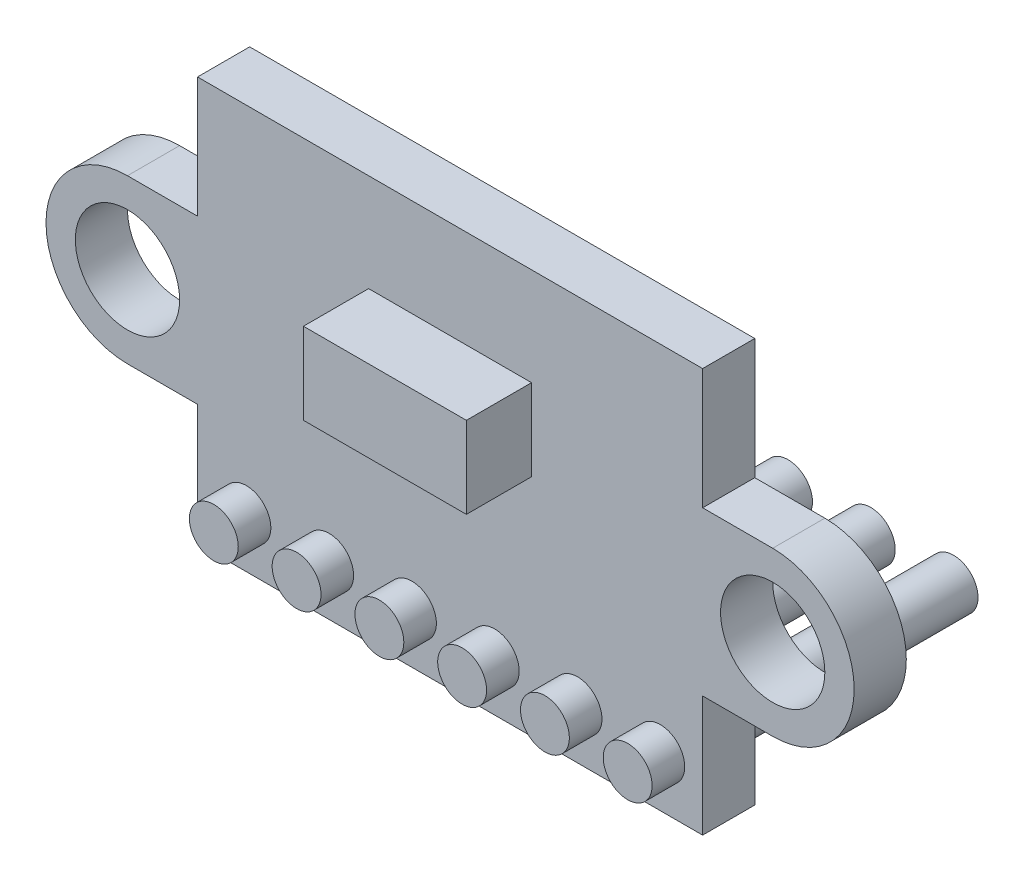
SolidWorks part; units mm, degrees
ref_plane "Front Plane" through (0, 0, 0) normal (0, 0, 1) x (1, 0, 0)
ref_plane "Top Plane" through (0, 0, 0) normal (0, 1, 0) x (1, 0, 0)
ref_plane "Right Plane" through (0, 0, 0) normal (1, 0, 0) x (0, 0, -1)
sketch "Sketch1" plane through (0, 0, 0) normal (0, 0, 1) x (1, 0, 0)
  line L0 (-7.75, 6.2) -> (7.75, 6.2)
  line L1 (7.75, 6.2) -> (7.75, 2.5)
  line L2 (7.75, 2.5) -> (9.9, 2.5)
  line L3 (9.9, -2.5) -> (7.75, -2.5)
  line L4 (7.75, -2.5) -> (7.75, -6.2)
  line L5 (7.75, -6.2) -> (-7.75, -6.2)
  line L6 (-7.75, -6.2) -> (-7.75, -2.5)
  line L7 (-7.75, -2.5) -> (-9.9, -2.5)
  line L8 (-7.75, 6.2) -> (-7.75, 2.5)
  line L9 (-7.75, 2.5) -> (-9.9, 2.5)
  line L10 (-9.9, 0) -> (9.9, 0) construction
  line L11 (-7.75, 6.2) -> (7.75, -6.2) construction
  arc A0 (9.9, 2.5) -> (9.9, -2.5) centre (9.9, 0) cw
  arc A1 (-9.9, 2.5) -> (-9.9, -2.5) centre (-9.9, 0) ccw
  circle A2 centre (-9.9, 0) radius 1.6
  circle A3 centre (9.9, 0) radius 1.6
  point P17 (-0.5364, 6.1018)
  point P21 (0, 0)
  dimension "D2" = 3.2
  dimension "D4" = 2.5
  dimension "D1" = 15.5
  dimension "D3" = 12.4
  dimension "D5" = 19.8
  dimension "D6" = 6.2
extrude "Main" add sketch "Sketch1" along normal blind 1.6
sketch "Sketch2" plane through (0, 0, 1.6) normal (0, 0, 1) x (1, 0, 0)
  line L0 (7.75, 6.2) -> (-7.75, 6.2) construction
  line L1 (-2.5, 3.2) -> (2.5, 3.2)
  line L2 (-2.5, 3.2) -> (-2.5, 0.7)
  line L3 (-2.5, 0.7) -> (2.5, 0.7)
  line L4 (2.5, 3.2) -> (2.5, 0.7)
  line L5 (-7.75, 6.2) -> (-7.75, 2.5) construction
  dimension "D1" = 5
  dimension "D2" = 3
  dimension "D3" = 2.5
  dimension "D4" = 5.25
extrude "Sensor" add sketch "Sketch2" along normal blind 2
ref_plane "Plane1" through (0, 0, 2.6) normal (0, 0, 1) x (1, 0, 0)
sketch "Sketch3" plane through (0, 0, 2.6) normal (0, 0, 1) x (1, 0, 0)
  line L0 (-7.75, -6.2) -> (7.75, -6.2) construction
  line L1 (-7.75, -2.5) -> (-7.75, -6.2) construction
  circle A0 centre (-6.25, -4.66) radius 0.75
  dimension "D3" = 1.5
  dimension "D1" = 1.54
  dimension "D2" = 1.5
extrude "Cables" add sketch "Sketch3" against normal blind 10
pattern_linear "LPattern1" count 6 spacing 2.54 along (1, 0, 0) of "Cables"
